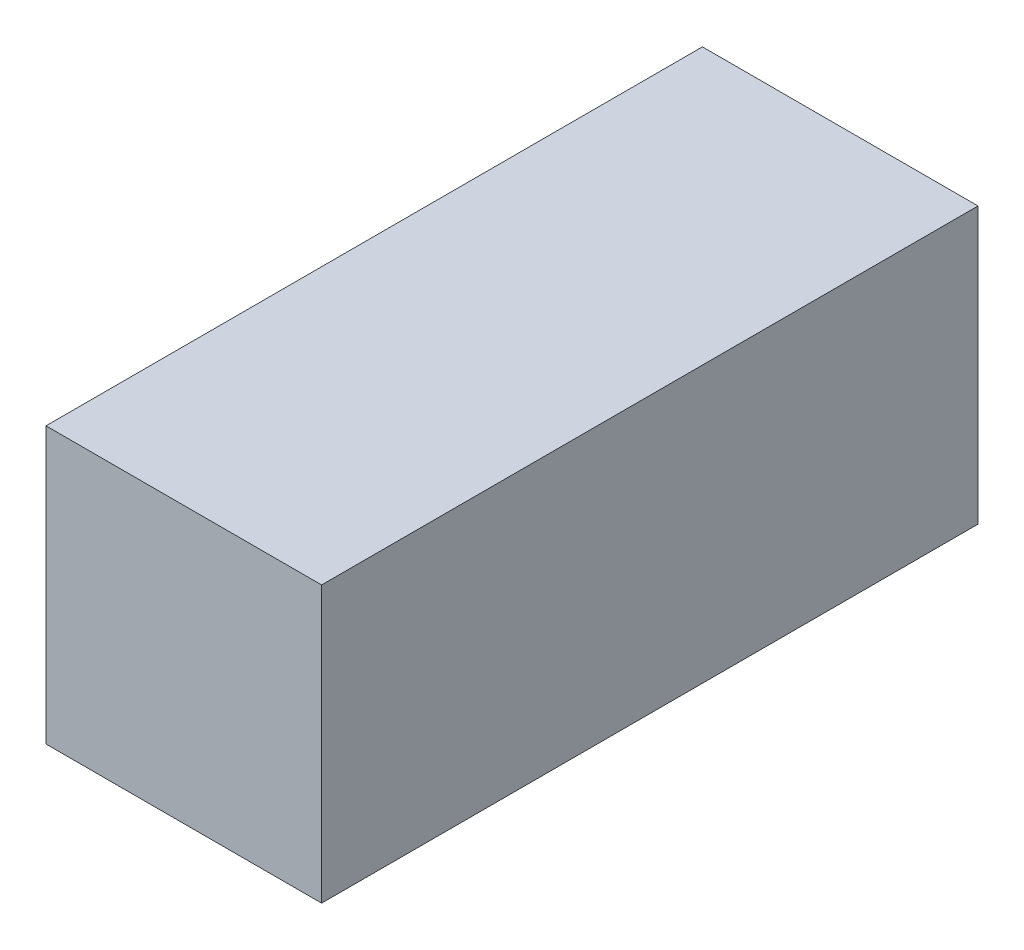
SolidWorks part; units mm, degrees
ref_plane "Piano frontale" through (0, 0, 0) normal (0, 0, 1) x (1, 0, 0)
ref_plane "Piano superiore" through (0, 0, 0) normal (0, 1, 0) x (1, 0, 0)
ref_plane "Piano destro" through (0, 0, 0) normal (1, 0, 0) x (0, 0, -1)
sketch "Schizzo1" plane through (0, 0, 0) normal (0, 0, 1) x (1, 0, 0)
  line L1 (33.5876, 33.5876) -> (-33.5876, 33.5876)
  line L2 (-33.5876, 33.5876) -> (-33.5876, -33.5876)
  line L3 (-33.5876, -33.5876) -> (33.5876, -33.5876)
  line L4 (33.5876, -33.5876) -> (33.5876, 33.5876)
  circle A0 centre (0, 0) radius 33.5876 construction
  dimension "D1" = 47.5
extrude "Estrusione-Estrusione1" add sketch "Schizzo1" along normal blind 160
